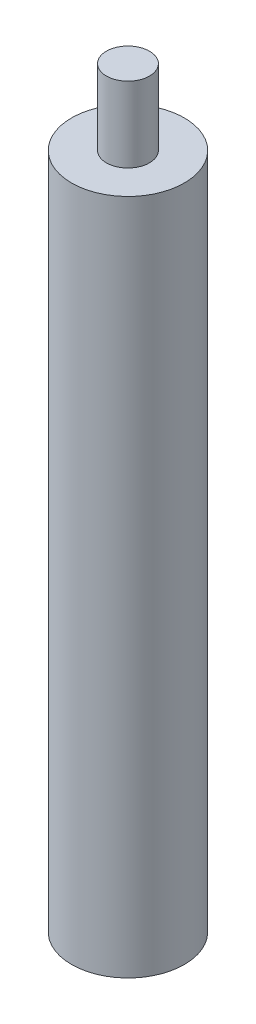
SolidWorks part; units mm, degrees
ref_plane "Front Plane" through (0, 0, 0) normal (0, 0, 1) x (1, 0, 0)
ref_plane "Top Plane" through (0, 0, 0) normal (0, 1, 0) x (1, 0, 0)
ref_plane "Right Plane" through (0, 0, 0) normal (1, 0, 0) x (0, 0, -1)
sketch "Sketch1" plane through (0, 0, 0) normal (0, 1, 0) x (1, 0, 0)
  circle A0 centre (0, 0) radius 9.525
  dimension "D1" = 19.05
extrude "Boss-Extrude1" add sketch "Sketch1" along normal blind 114.3
sketch "Sketch2" plane through (0, 114.3, 0) normal (0, 1, 0) x (1, 0, 0)
  circle A0 centre (0, 0) radius 3.6386
  dimension "D1" = 7.2771
extrude "Boss-Extrude2" add sketch "Sketch2" along normal blind 12.7
ref_plane "Plane1" through (0, 57.15, 0) normal (0, 1, 0) x (1, 0, 0)
sketch "Sketch3" plane through (0, 0, 0) normal (0, -1, 0) x (1, 0, 0)
  circle A0 centre (0, 0) radius 3.5116
  dimension "D1" = 7.0231
extrude "Cut-Extrude1" cut sketch "Sketch3" against normal blind 12.7
